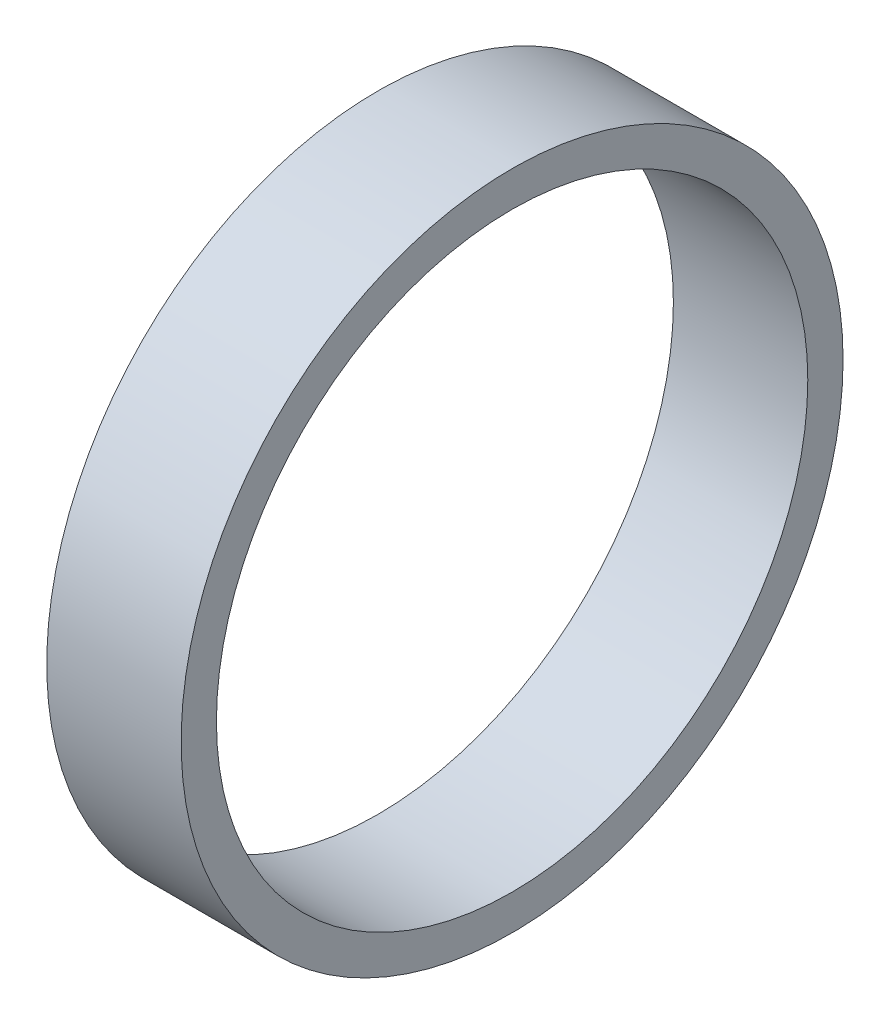
SolidWorks part; units mm, degrees
ref_plane "前视基准面" through (0, 0, 0) normal (0, 0, 1) x (1, 0, 0)
ref_plane "上视基准面" through (0, 0, 0) normal (0, 1, 0) x (1, 0, 0)
ref_plane "右视基准面" through (0, 0, 0) normal (1, 0, 0) x (0, 0, -1)
sketch "草图1" plane through (0, 0, 0) normal (1, 0, 0) x (0, 0, -1)
  circle A0 centre (0, 0) radius 4.925
  circle A1 centre (0, 0) radius 4.4
  dimension "D1" = 9.85
  dimension "D2" = 8.8
extrude "凸台-拉伸1" add sketch "草图1" along normal blind 2
